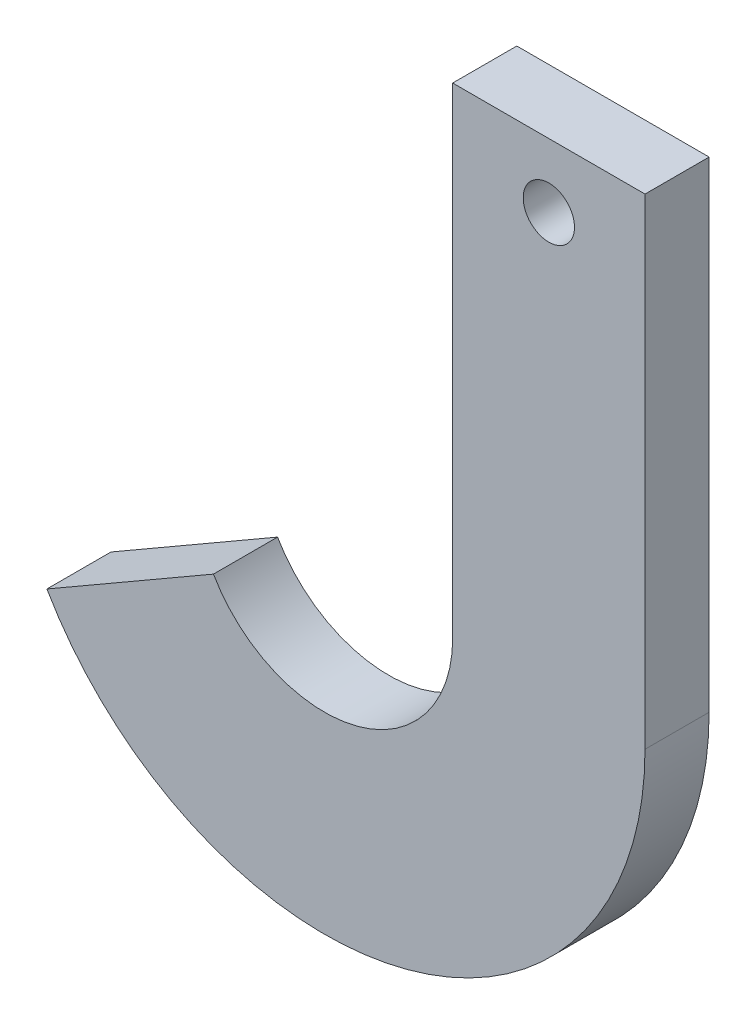
SolidWorks part; units mm, degrees
material "AISI 1010 Steel, hot rolled bar"
ref_plane "Front Plane" through (0, 0, 0) normal (0, 0, 1) x (1, 0, 0)
ref_plane "Top Plane" through (0, 0, 0) normal (0, 1, 0) x (1, 0, 0)
ref_plane "Right Plane" through (0, 0, 0) normal (1, 0, 0) x (0, 0, -1)
sketch "Sketch1" plane through (0, 0, 0) normal (0, 0, 1) x (1, 0, 0)
  line L0 (-34.641, -20) -> (-86.6025, -50)
  line L1 (100, 0) -> (100, 150)
  line L2 (40, 150) -> (40, 0)
  line L3 (40, 150) -> (100, 150)
  line L4 (0, 0) -> (-155.1085, 0) construction
  arc A0 (-34.641, -20) -> (40, 0) centre (0, 0) ccw
  arc A1 (-86.6025, -50) -> (100, 0) centre (0, 0) ccw
  dimension "D1" = 40
  dimension "D2" = 100
  dimension "D3" = 60
  dimension "D4" = 60
  dimension "D5" = 150
  dimension "D6" = 30
extrude "Extrude1" add sketch "Sketch1" along normal blind 20
sketch "Sketch2" plane through (0, 0, 0) normal (0, 0, 1) x (1, 0, 0)
  line L0 (100, 150) -> (40, 150) construction
  line L1 (40, 150) -> (40, 0) construction
  circle A0 centre (70, 130) radius 8
  dimension "D1" = 16
  dimension "D2" = 20
  dimension "D3" = 30
extrude "Extrude3" cut sketch "Sketch2" along normal through all
ref_plane "Plane1" through (76, 0, 0) normal (1, 0, 0) x (0, 0, -1)
split line "Split Line1"
sketch "Sketch3" plane through (0, 0, 0) normal (0, 0, 1) x (1, 0, 0)
  line L0 (0, 0) -> (0, -121.8357)
  arc A0 (-34.641, -20) -> (40, 0) centre (0, 0) ccw construction
  arc A1 (-34.641, -20) -> (40, 0) centre (0, 0) ccw
  point P5 (0, 0)
  point P6 (0, -121.8357)
